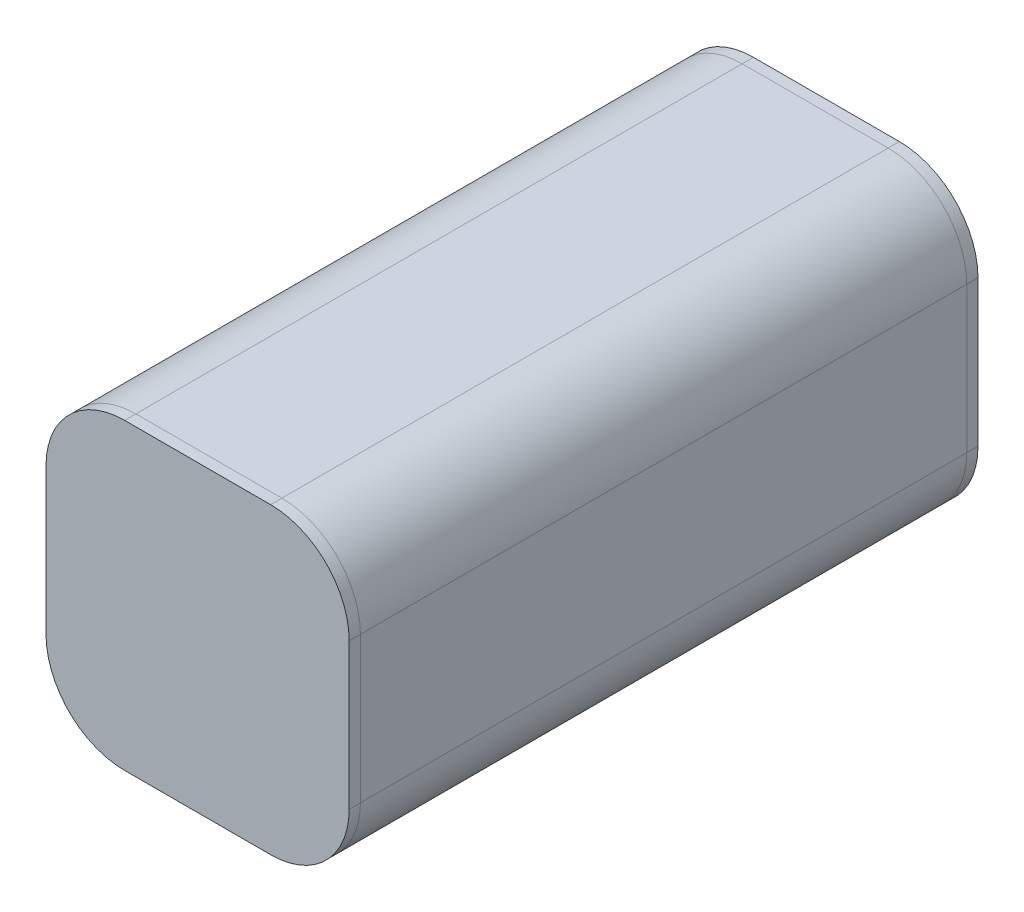
SolidWorks part; units mm, degrees
ref_plane "Front Plane" through (0, 0, 0) normal (0, 0, 1) x (1, 0, 0)
ref_plane "Top Plane" through (0, 0, 0) normal (0, 1, 0) x (1, 0, 0)
ref_plane "Right Plane" through (0, 0, 0) normal (1, 0, 0) x (0, 0, -1)
sketch "Sketch2" plane through (0, 0, 0) normal (0, 0, 1) x (1, 0, 0)
  line L0 (-8.255, 8.255) -> (8.255, -8.255) construction
  line L1 (-8.255, -8.255) -> (8.255, 8.255) construction
  circle A0 centre (-8.255, -8.255) radius 8.255
  circle A1 centre (8.255, -8.255) radius 8.255
  circle A2 centre (8.255, 8.255) radius 8.255
  circle A3 centre (-8.255, 8.255) radius 8.255
  dimension "D1" = 16.51
extrude "Extrude1" add sketch "Sketch2" along normal mid plane 68.58 contours A0 | A1 | A2 | A3
sketch "Sketch3" plane through (0, 0, 34.29) normal (0, 0, 1) x (1, 0, 0)
  line L0 (-16.51, 8.255) -> (-16.51, -8.255)
  line L1 (-8.255, -16.51) -> (8.255, -16.51)
  line L2 (16.51, -8.255) -> (16.51, 8.255)
  line L3 (8.255, 16.51) -> (-8.255, 16.51)
  line L4 (8.255, 17.145) -> (-8.255, 17.145)
  line L5 (-17.145, 8.255) -> (-17.145, -8.255)
  line L6 (-8.255, -17.145) -> (8.255, -17.145)
  line L7 (17.145, -8.255) -> (17.145, 8.255)
  circle A0 centre (-8.255, 8.255) radius 8.255 construction
  circle A1 centre (8.255, 8.255) radius 8.255 construction
  circle A2 centre (-8.255, -8.255) radius 8.255 construction
  circle A3 centre (8.255, -8.255) radius 8.255 construction
  arc A4 (-8.255, 16.51) -> (-16.51, 8.255) centre (-8.255, 8.255) ccw
  arc A5 (16.51, 8.255) -> (8.255, 16.51) centre (8.255, 8.255) ccw
  arc A6 (8.255, -16.51) -> (16.51, -8.255) centre (8.255, -8.255) ccw
  arc A7 (-16.51, -8.255) -> (-8.255, -16.51) centre (-8.255, -8.255) ccw
  arc A8 (-8.255, 17.145) -> (-17.145, 8.255) centre (-8.255, 8.255) ccw
  arc A9 (-17.145, -8.255) -> (-8.255, -17.145) centre (-8.255, -8.255) ccw
  arc A10 (8.255, -17.145) -> (17.145, -8.255) centre (8.255, -8.255) ccw
  arc A11 (17.145, 8.255) -> (8.255, 17.145) centre (8.255, 8.255) ccw
  dimension "D1" = 8.255
  dimension "D2" = 0.635
extrude "Extrude2" add sketch "Sketch3" against normal blind 68.58 separate body
sketch "Sketch4" plane through (0, 0, 34.29) normal (0, 0, 1) x (1, 0, 0)
  line L9 (8.255, 17.145) -> (-8.255, 17.145)
  line L10 (-17.145, 8.255) -> (-17.145, -8.255)
  line L11 (-8.255, -17.145) -> (8.255, -17.145)
  line L12 (17.145, -8.255) -> (17.145, 8.255)
  line L13 (8.255, 17.145) -> (-8.255, 17.145)
  line L14 (-17.145, 8.255) -> (-17.145, -8.255)
  line L15 (-8.255, -17.145) -> (8.255, -17.145)
  line L16 (17.145, -8.255) -> (17.145, 8.255)
  arc A8 (17.145, 8.255) -> (8.255, 17.145) centre (8.255, 8.255) ccw
  arc A9 (-8.255, 17.145) -> (-17.145, 8.255) centre (-8.255, 8.255) ccw
  arc A10 (-17.145, -8.255) -> (-8.255, -17.145) centre (-8.255, -8.255) ccw
  arc A11 (8.255, -17.145) -> (17.145, -8.255) centre (8.255, -8.255) ccw
  arc A12 (17.145, 8.255) -> (8.255, 17.145) centre (8.255, 8.255) ccw
  arc A13 (-8.255, 17.145) -> (-17.145, 8.255) centre (-8.255, 8.255) ccw
  arc A14 (-17.145, -8.255) -> (-8.255, -17.145) centre (-8.255, -8.255) ccw
  arc A15 (8.255, -17.145) -> (17.145, -8.255) centre (8.255, -8.255) ccw
  dimension "D1" = 0
extrude "Boss-Extrude2" add sketch "Sketch4" along normal blind 1.27 separate body
mirror "Mirror1" about plane through (0, 0, 0) normal (0, 0, 1) of bodies 106
